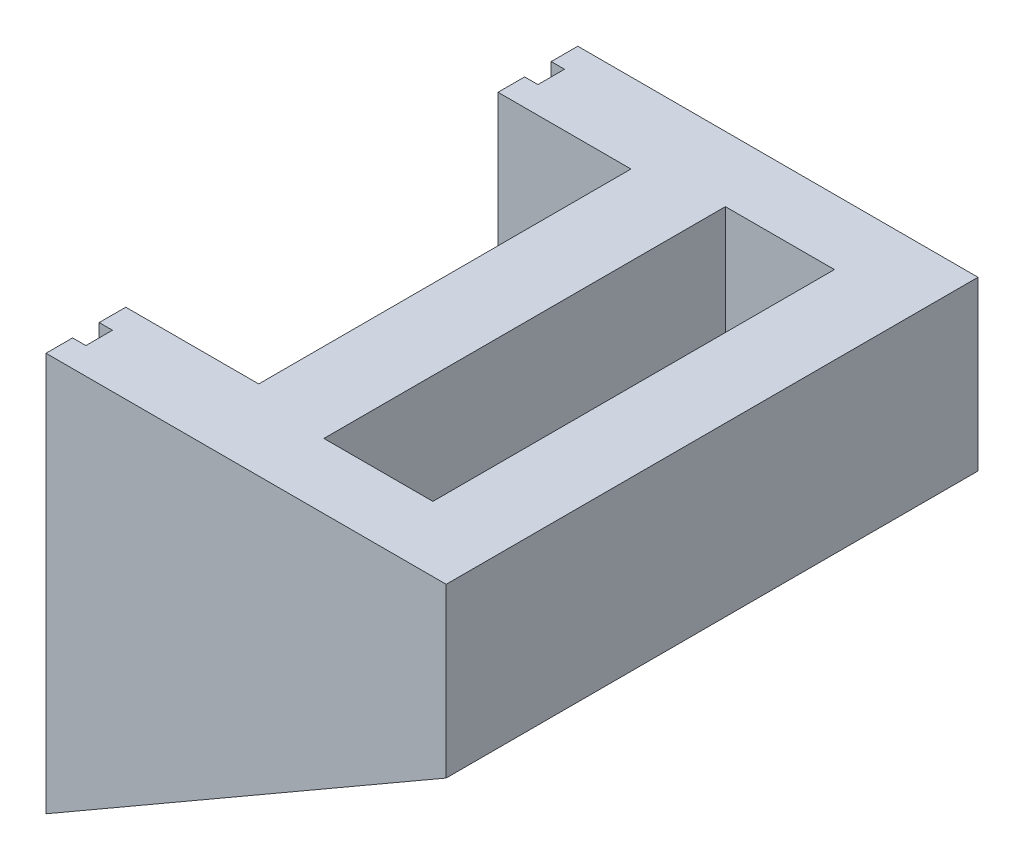
SolidWorks part; units mm, degrees
ref_plane "Front Plane" through (0, 0, 0) normal (0, 0, 1) x (1, 0, 0)
ref_plane "Top Plane" through (0, 0, 0) normal (0, 1, 0) x (1, 0, 0)
ref_plane "Right Plane" through (0, 0, 0) normal (1, 0, 0) x (0, 0, -1)
sketch "Sketch2" plane through (0, 0, 0) normal (0, 1, 0) x (1, 0, 0)
  line L1 (-5, -10) -> (5, -10)
  line L2 (-5, -10) -> (-5, 10)
  line L3 (-5, 10) -> (5, 10)
  line L4 (5, -10) -> (5, 10)
  line L5 (-5, -10) -> (5, 10) construction
  line L6 (-5, 10) -> (5, -10) construction
  point P0 (0, 0)
  dimension "D1" = 10
  dimension "D2" = 20
extrude "Boss-Extrude1" add sketch "Sketch2" along normal blind 15
sketch "Sketch3" plane through (0, 15, 0) normal (0, 1, 0) x (1, 0, 0)
  line L1 (-2.05, -7.55) -> (2.05, -7.55)
  line L2 (-2.05, -7.55) -> (-2.05, 7.55)
  line L3 (-2.05, 7.55) -> (2.05, 7.55)
  line L4 (2.05, -7.55) -> (2.05, 7.55)
  line L5 (-2.05, -7.55) -> (2.05, 7.55) construction
  line L6 (-2.05, 7.55) -> (2.05, -7.55) construction
  point P1 (0, 0)
  dimension "D1" = 4.1
  dimension "D2" = 15.1
extrude "Cut-Extrude1" cut sketch "Sketch3" against normal through all
sketch "Sketch4" plane through (0, 15, 0) normal (0, 1, 0) x (1, 0, 0)
  line L1 (-5, 10) -> (-2.05, 10)
  line L2 (-5, 10) -> (-5, -7.55)
  line L4 (-2.05, 10) -> (-2.05, -7.55)
  line L5 (-2.05, -7.55) -> (-5, -7.55)
  line L6 (-2.05, -7.55) -> (-2.05, -10)
  line L7 (-2.05, -10) -> (-5, -10)
  line L8 (-5, -7.55) -> (-5, -10)
  line M4 (-2.05, -7.55) -> (-2.05, 7.55)
  line M6 (5, 10) -> (-5, 10)
  line M7 (-5, 10) -> (-5, -10)
  line M8 (-5, -10) -> (5, -10)
extrude "Cut-Extrude2" cut sketch "Sketch4" against normal blind 15 contours L5 L4 M4 M6 M7 | L6 L5 M7 M8
sketch "Sketch6" plane through (-2.05, 0, 0) normal (-1, 0, 0) x (0, 0, 1)
  line L1 (10, 15) -> (-10, 15)
  line L2 (10, 15) -> (10, 0)
  line L3 (10, 0) -> (-10, 0)
  line L4 (-10, 15) -> (-10, 0)
extrude "Boss-Extrude2" add sketch "Sketch6" along normal blind 3
sketch "Sketch8" plane through (-5.05, 0, 0) normal (-1, 0, 0) x (0, 0, 1)
  line L0 (0, 0) -> (0, 15) construction
  line L1 (10, 15) -> (-10, 15) construction
  line L2 (-7, 15) -> (-10, 15)
  line L3 (-10, 15) -> (-10, 0)
  line L4 (-10, 0) -> (10, 0)
  line L5 (-7, 15) -> (-7, 3)
  line L6 (-7, 3) -> (7, 3)
  line L7 (10, 15) -> (10, 0)
  line L8 (7, 15) -> (10, 15)
  line L9 (7, 15) -> (7, 3)
  point P14 (0, 3)
  dimension "D1" = 3
  dimension "D2" = 3
extrude "Boss-Extrude3" add sketch "Sketch8" along normal blind 5
sketch "Sketch10" plane through (0, 0, 10) normal (0, 0, 1) x (1, 0, 0)
  line L0 (-10.05, 0) -> (5, 8.6891) construction
  line L1 (5, 15) -> (5, 0) construction
  line L2 (-10.05, 0) -> (5, 0) construction
  line L3 (-10.05, 0) -> (5, 8.6891)
  line L4 (5, 8.6891) -> (5, 0)
  line L5 (5, 0) -> (-10.05, 0)
  dimension "D1" = 30
extrude "Cut-Extrude3" cut sketch "Sketch10" against normal through all
sketch "Sketch11" plane through (-10.05, 0, 0) normal (-1, 0, 0) x (0, 0, 1)
  line L0 (0, 0) -> (0, 3) construction
  line L1 (7, 3) -> (-7, 3) construction
  line L2 (0, 1.5) -> (-8.5, 1.5) construction
  line L3 (-8, 15) -> (-8, 2)
  line L4 (-8.5, 15) -> (-8.5, 1.5) construction
  line L5 (-7, 15) -> (-10, 15) construction
  line L6 (0, 2) -> (-8, 2)
  line L7 (-9, 15) -> (-9, 1)
  line L8 (0, 1) -> (-9, 1)
  line L9 (-9, 15) -> (-8, 15)
  line L10 (-8, 15) -> (-8.0353, 15.0079)
  line L11 (0, 1) -> (9, 1)
  line L12 (0, 2) -> (8, 2)
  line L13 (9, 15) -> (9, 1)
  line L14 (9, 15) -> (8, 15)
  line L15 (8, 15) -> (8, 2)
  line L16 (8, 15) -> (8.0353, 15.0079)
  line M10 (-7, 15) -> (-10, 15)
  line M14 (10, 15) -> (7, 15)
  dimension "D1" = 0.5
  dimension "D2" = 0.5
extrude "Cut-Extrude4" cut sketch "Sketch11" against normal blind 0.5 contours L15 L12 L6 L3 L7 L8 L11 L13 M14 M10
